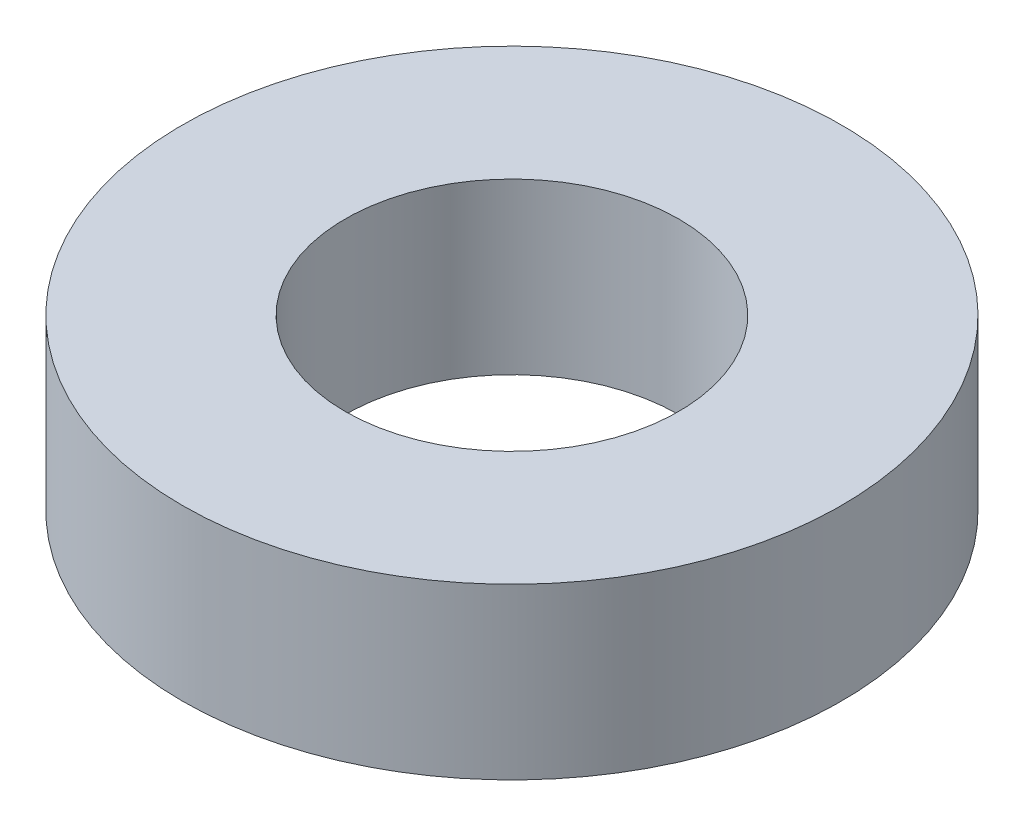
SolidWorks part; units mm, degrees
ref_plane "Front Plane" through (0, 0, 0) normal (0, 0, 1) x (1, 0, 0)
ref_plane "Top Plane" through (0, 0, 0) normal (0, 1, 0) x (1, 0, 0)
ref_plane "Right Plane" through (0, 0, 0) normal (1, 0, 0) x (0, 0, -1)
sketch "Sketch1" plane through (0, 0, 0) normal (0, 1, 0) x (1, 0, 0)
  circle A0 centre (0, 0) radius 12.5
  circle A1 centre (0, 0) radius 24.7
extrude "Boss-Extrude1" add sketch "Sketch1" against normal blind 12.7
